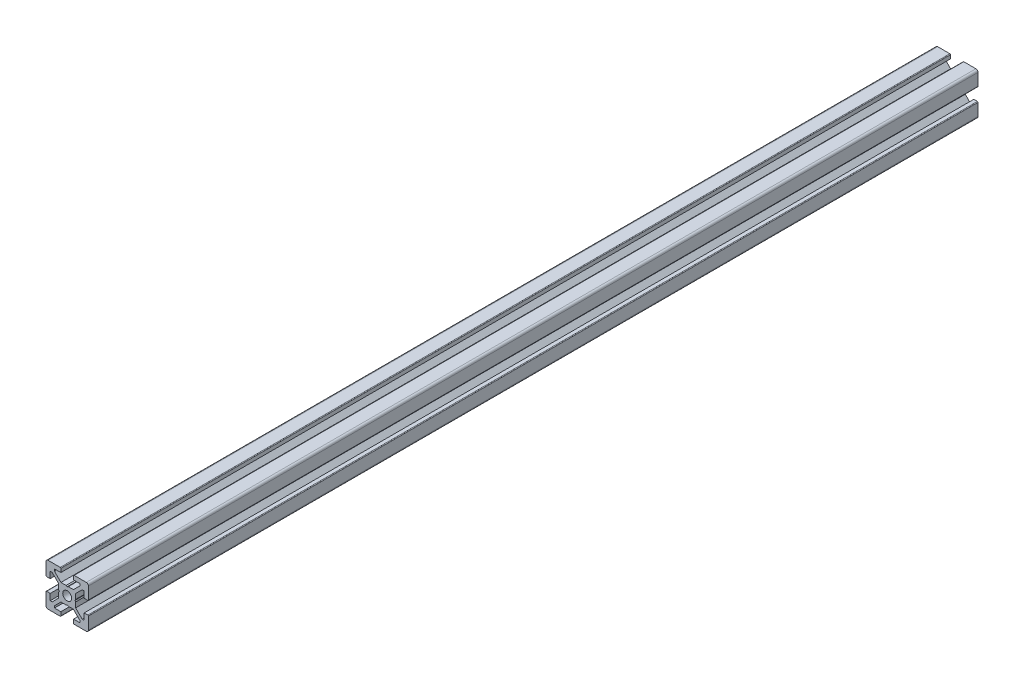
SolidWorks part; units mm, degrees
ref_plane "Front Plane" through (0, 0, 0) normal (0, 0, 1) x (1, 0, 0)
ref_plane "Top Plane" through (0, 0, 0) normal (0, 1, 0) x (1, 0, 0)
ref_plane "Right Plane" through (0, 0, 0) normal (1, 0, 0) x (0, 0, -1)
ref_plane "Plane1" through (0, 0, 0) normal (0, 0, 1) x (1, 0, 0)
sketch "Sketch1" plane through (0, 0, 0) normal (0, 0, 1) x (1, 0, 0)
  line L0 (-10, 9) -> (-10, 3.3)
  line L1 (-9.7, 3) -> (-8, 3)
  line L2 (-8, 3) -> (-8, 6)
  line L3 (-8, 6) -> (-7.0607, 6)
  line L4 (-7.0607, 6) -> (-4, 2.9393)
  line L5 (-4, 2.9393) -> (-4, 0.5196)
  line L6 (-4, 0.5196) -> (-3.7, 0)
  line L7 (-3.7, 0) -> (-4, -0.5196)
  line L8 (-4, -0.5196) -> (-4, -2.9393)
  line L9 (-4, -2.9393) -> (-7.0607, -6)
  line L10 (-7.0607, -6) -> (-8, -6)
  line L11 (-8, -6) -> (-8, -3)
  line L12 (-8, -3) -> (-9.7, -3)
  line L13 (-10, -3.3) -> (-10, -9)
  line L14 (-9, -10) -> (-3.3, -10)
  line L15 (-3, -9.7) -> (-3, -8)
  line L16 (-3, -8) -> (-6, -8)
  line L17 (-6, -8) -> (-6, -7.0607)
  line L18 (-6, -7.0607) -> (-2.9393, -4)
  line L19 (-2.9393, -4) -> (-0.5196, -4)
  line L20 (-0.5196, -4) -> (0, -3.7)
  line L21 (0, -3.7) -> (0.5196, -4)
  line L22 (0.5196, -4) -> (2.9393, -4)
  line L23 (2.9393, -4) -> (6, -7.0607)
  line L24 (6, -7.0607) -> (6, -8)
  line L25 (6, -8) -> (3, -8)
  line L26 (3, -8) -> (3, -9.7)
  line L27 (3.3, -10) -> (9, -10)
  line L28 (10, -9) -> (10, -3.3)
  line L29 (9.7, -3) -> (8, -3)
  line L30 (8, -3) -> (8, -6)
  line L31 (8, -6) -> (7.0606, -6)
  line L32 (7.0606, -6) -> (4, -2.9393)
  line L33 (4, -2.9393) -> (4, -0.5196)
  line L34 (4, -0.5196) -> (3.7, 0)
  line L35 (3.7, 0) -> (4, 0.5196)
  line L36 (4, 0.5196) -> (4, 2.9393)
  line L37 (4, 2.9393) -> (7.0607, 6)
  line L38 (7.0607, 6) -> (8, 6)
  line L39 (8, 6) -> (8, 3)
  line L40 (8, 3) -> (9.7, 3)
  line L41 (10, 3.3) -> (10, 9)
  line L42 (9, 10) -> (3.3, 10)
  line L43 (3, 9.7) -> (3, 8)
  line L44 (3, 8) -> (6, 8)
  line L45 (6, 8) -> (6, 7.0607)
  line L46 (6, 7.0607) -> (2.9393, 4)
  line L47 (2.9393, 4) -> (0.5196, 4)
  line L48 (0.5196, 4) -> (0, 3.7)
  line L49 (0, 3.7) -> (-0.5196, 4)
  line L50 (-0.5196, 4) -> (-2.9394, 4)
  line L51 (-2.9394, 4) -> (-6, 7.0606)
  line L52 (-6, 7.0606) -> (-6, 8)
  line L53 (-6, 8) -> (-3, 8)
  line L54 (-3, 8) -> (-3, 9.7)
  line L55 (-3.3, 10) -> (-9, 10)
  arc A0 (-10, 3.3) -> (-9.7, 3) centre (-9.7, 3.3) ccw
  arc A1 (-9.7, -3) -> (-10, -3.3) centre (-9.7, -3.3) ccw
  arc A2 (-10, -9) -> (-9, -10) centre (-9, -9) ccw
  arc A3 (-3.3, -10) -> (-3, -9.7) centre (-3.3, -9.7) ccw
  arc A4 (3, -9.7) -> (3.3, -10) centre (3.3, -9.7) ccw
  arc A5 (9, -10) -> (10, -9) centre (9, -9) ccw
  arc A6 (10, -3.3) -> (9.7, -3) centre (9.7, -3.3) ccw
  arc A7 (9.7, 3) -> (10, 3.3) centre (9.7, 3.3) ccw
  arc A8 (10, 9) -> (9, 10) centre (9, 9) ccw
  arc A9 (3.3, 10) -> (3, 9.7) centre (3.3, 9.7) ccw
  arc A10 (-3, 9.7) -> (-3.3, 10) centre (-3.3, 9.7) ccw
  arc A11 (-9, 10) -> (-10, 9) centre (-9, 9) ccw
  circle A12 centre (0, 0) radius 2.1
  dimension "D1" = 4.2
  dimension "D2" = 20
  dimension "D3" = 6
  dimension "D4" = 7
  dimension "D5" = 2
  dimension "D6" = 6
extrude "Boss-Extrude1" add sketch "Sketch1" against normal blind 420
